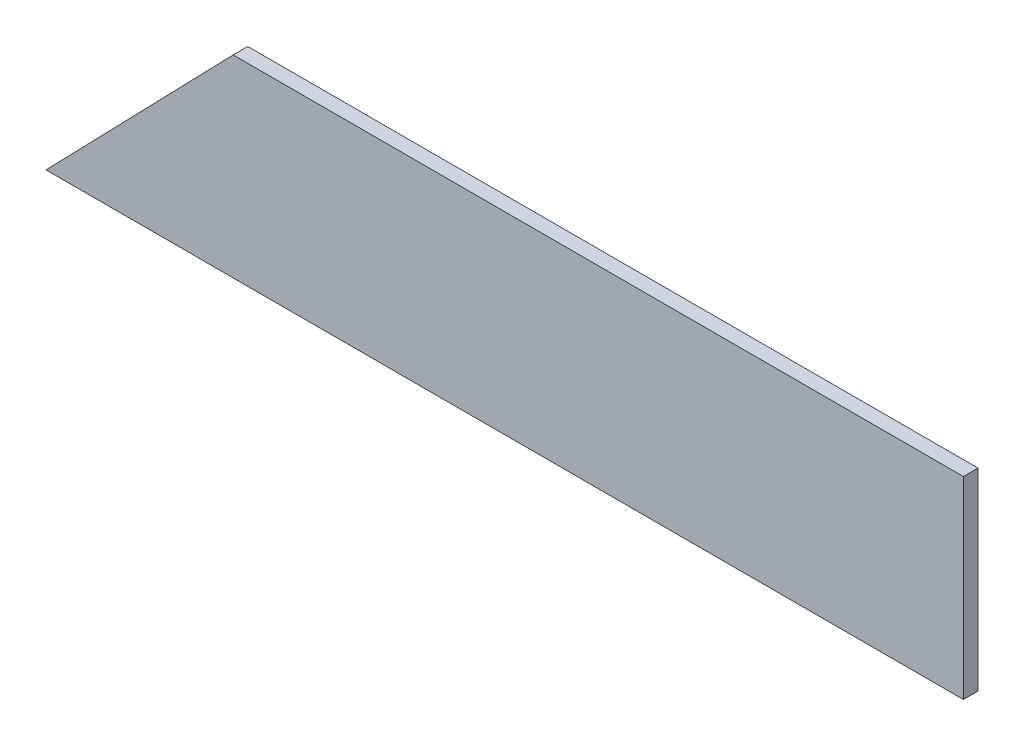
SolidWorks part; units mm, degrees
material "Pine"
ref_plane "Front Plane" through (0, 0, 0) normal (0, 0, 1) x (1, 0, 0)
ref_plane "Top Plane" through (0, 0, 0) normal (0, 1, 0) x (1, 0, 0)
ref_plane "Right Plane" through (0, 0, 0) normal (1, 0, 0) x (0, 0, -1)
sketch "Sketch1" plane through (0, 0, 0) normal (0, 0, 1) x (1, 0, 0)
  line L0 (-338.8259, -50.4066) -> (-104.9899, 190.8934)
  line L1 (-104.9899, 190.8934) -> (807.3491, 190.8934)
  line L3 (-338.8259, -50.4066) -> (807.3491, -50.4066)
  line L4 (807.3491, 190.8934) -> (807.3491, -50.4066)
  dimension "D1" = 241.3
  dimension "D2" = 1146.175
  dimension "D3" = 45.9
  dimension "D4" = 912.339
extrude "Boss-Extrude1" add sketch "Sketch1" along normal blind 18.2562
sketch "Sketch2" plane through (807.3491, 0, 0) normal (1, 0, 0) x (0, 0, -1)
  line L0 (0, -50.4066) -> (0, -68.1866) construction
  line L1 (0, -50.4066) -> (0, 8.5214)
  line L2 (0, -50.4066) -> (0, 190.8934) construction
  line L3 (0, 8.5214) -> (-18.4725, -68.4222)
  line L4 (-18.4725, -68.4222) -> (0, -68.1866)
  dimension "D1" = 17.78
  dimension "D2" = 58.928
  dimension "D3" = 13.5
extrude "Cut-Extrude1" [suppressed] cut sketch "Sketch2" against normal through all and the other way through all
chamfer "Chamfer1" [suppressed] distance 63.5 angle 15
